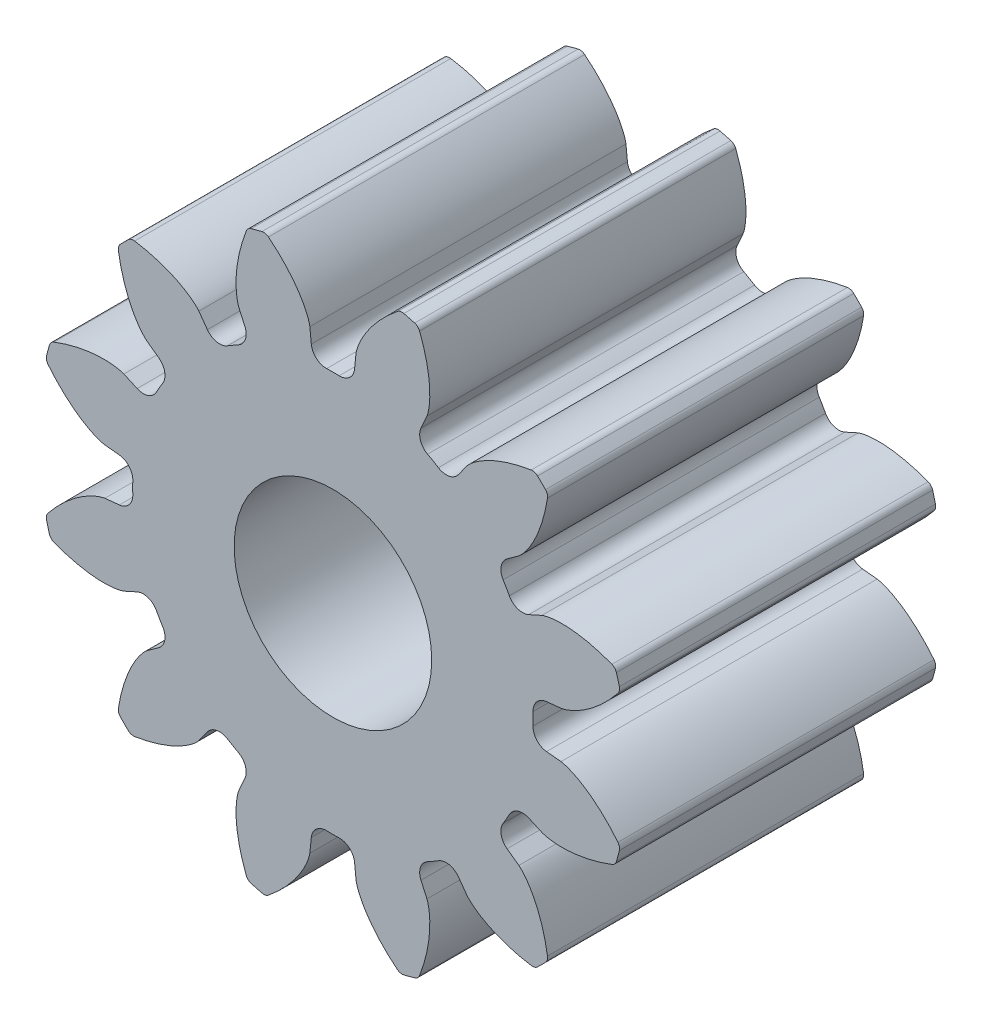
SolidWorks part; units mm, degrees
material "DELRIN"
ref_plane "Front" through (0, 0, 0) normal (0, 0, 1) x (1, 0, 0)
ref_plane "Top" through (0, 0, 0) normal (0, 1, 0) x (1, 0, 0)
ref_plane "Right" through (0, 0, 0) normal (1, 0, 0) x (0, 0, -1)
sketch "Sketch1" plane through (0, 0, 0) normal (0, 0, 1) x (1, 0, 0)
  circle A0 centre (0, 0) radius 11.8533
extrude "Boss-Extrude1" add sketch "Sketch1" along normal blind 12.7
sketch "Sketch3" plane through (0, 0, 0) normal (0, 0, 1) x (1, 0, 0)
  line L0 (0, 0) -> (43.7181, 0) construction
  line L2 (0, 0) -> (-0.8104, 8.0024) construction
  line L3 (0, 0) -> (0.8104, 8.0024) construction
  line L4 (0.8104, 8.0024) -> (0.9277, 9.1612) construction
  line L5 (0, 0) -> (0, 61.276) construction
  line L6 (-0.8104, 8.0024) -> (-0.9277, 9.1612) construction
  circle A0 centre (0, 0) radius 11.8533 construction
  circle A1 centre (0, 0) radius 10.16 construction
  circle A2 centre (0, 0) radius 9.2081 construction
  arc A3 (0.8104, 8.0024) -> (-0.8104, 8.0024) centre (0, 0) ccw construction
  arc A5 (2.7064, 11.5402) -> (-2.7064, 11.5402) centre (0, 0) ccw
  spline S0 degree 4 poles (-0.9277, 9.1612) (-0.9283, 9.1657) (-0.93, 9.1781) (-0.9342, 9.2015) (-0.9423, 9.2394) (-0.9545, 9.2874) (-0.9726, 9.3489) (-0.9967, 9.4206) (-1.026, 9.4987) (-1.0611, 9.5826) (-1.0988, 9.6655) (-1.1389, 9.7473) (-1.1812, 9.8279) (-1.235, 9.9246) (-1.3032, 10.0389) (-1.3882, 10.1702) (-1.4906, 10.3162) (-1.6015, 10.4617) (-1.7158, 10.602) (-1.8371, 10.7404) (-1.9586, 10.8719) (-2.0907, 11.0047) (-2.2156, 11.1255) (-2.3617, 11.2564) (-2.4815, 11.3607) (-2.6459, 11.4936) (-2.7449, 11.5706) (-2.863, 11.659) (-2.9166, 11.6974) (-2.9495, 11.721) knots 0 0 0 0 0 0.005377 0.015084 0.028532 0.04661 0.064855 0.092111 0.119476 0.146842 0.174209 0.201575 0.228941 0.256307 0.307035 0.361767 0.4165 0.471232 0.525964 0.580697 0.635429 0.690161 0.744894 0.799626 0.854358 0.909091 0.954545 1 1 1 1 1 construction
  spline S1 degree 4 poles (-0.9277, 9.1612) (-0.9283, 9.1657) (-0.93, 9.1781) (-0.9342, 9.2015) (-0.9423, 9.2394) (-0.9545, 9.2874) (-0.9726, 9.3489) (-0.9967, 9.4206) (-1.026, 9.4987) (-1.0611, 9.5826) (-1.0988, 9.6655) (-1.1389, 9.7473) (-1.1812, 9.8279) (-1.235, 9.9246) (-1.3032, 10.0389) (-1.3882, 10.1702) (-1.4906, 10.3162) (-1.6015, 10.4617) (-1.7158, 10.602) (-1.8371, 10.7404) (-1.9586, 10.8719) (-2.0907, 11.0047) (-2.2156, 11.1255) (-2.3617, 11.2564) (-2.4815, 11.3607) (-2.6102, 11.4648) (-2.6737, 11.5149) (-2.7064, 11.5402) knots 0 0 0 0 0 0.005377 0.015084 0.028532 0.04661 0.064855 0.092111 0.119476 0.146842 0.174209 0.201575 0.228941 0.256307 0.307035 0.361767 0.4165 0.471232 0.525964 0.580697 0.635429 0.690161 0.744894 0.799626 0.854358 0.909091 0.909091 0.909091 0.909091 0.909091
  spline S2 degree 4 poles (0.9277, 9.1612) (0.9283, 9.1657) (0.93, 9.1781) (0.9342, 9.2015) (0.9423, 9.2394) (0.9545, 9.2874) (0.9726, 9.3489) (0.9967, 9.4206) (1.026, 9.4987) (1.0611, 9.5826) (1.0988, 9.6655) (1.1389, 9.7473) (1.1812, 9.8279) (1.235, 9.9246) (1.3032, 10.0389) (1.3882, 10.1702) (1.4906, 10.3162) (1.6015, 10.4617) (1.7158, 10.602) (1.8371, 10.7404) (1.9586, 10.8719) (2.0907, 11.0047) (2.2156, 11.1255) (2.3617, 11.2564) (2.4815, 11.3607) (2.6459, 11.4936) (2.7449, 11.5706) (2.863, 11.659) (2.9166, 11.6974) (2.9495, 11.721) knots 0 0 0 0 0 0.005377 0.015084 0.028532 0.04661 0.064855 0.092111 0.119476 0.146842 0.174209 0.201575 0.228941 0.256307 0.307035 0.361767 0.4165 0.471232 0.525964 0.580697 0.635429 0.690161 0.744894 0.799626 0.854358 0.909091 0.954545 1 1 1 1 1 construction
  spline S3 degree 4 poles (0.9277, 9.1612) (0.9283, 9.1657) (0.93, 9.1781) (0.9342, 9.2015) (0.9423, 9.2394) (0.9545, 9.2874) (0.9726, 9.3489) (0.9967, 9.4206) (1.026, 9.4987) (1.0611, 9.5826) (1.0988, 9.6655) (1.1389, 9.7473) (1.1812, 9.8279) (1.235, 9.9246) (1.3032, 10.0389) (1.3882, 10.1702) (1.4906, 10.3162) (1.6015, 10.4617) (1.7158, 10.602) (1.8371, 10.7404) (1.9586, 10.8719) (2.0907, 11.0047) (2.2156, 11.1255) (2.3617, 11.2564) (2.4815, 11.3607) (2.6102, 11.4648) (2.6737, 11.5149) (2.7064, 11.5402) knots 0 0 0 0 0 0.005377 0.015084 0.028532 0.04661 0.064855 0.092111 0.119476 0.146842 0.174209 0.201575 0.228941 0.256307 0.307035 0.361767 0.4165 0.471232 0.525964 0.580697 0.635429 0.690161 0.744894 0.799626 0.854358 0.909091 0.909091 0.909091 0.909091 0.909091
  point P0 (0, 8.0433)
sketch "DCLTBC" plane through (0, 0, 0) normal (0, 0, 1) x (1, 0, 0)
  line L0 (0, 0) -> (41.04, 0) construction
  line L1 (-0.8104, 8.0024) -> (-0.9277, 9.1612) construction
  line L2 (0.8104, 8.0024) -> (0.9277, 9.1612) construction
  line L3 (-0.8104, 8.0024) -> (-0.9277, 9.1612)
  line L4 (0.8104, 8.0024) -> (0.9277, 9.1612)
  line L5 (0, 0) -> (0, 104.9356) construction
  circle A0 centre (0, 0) radius 11.8533
  circle A1 centre (0, 0) radius 10.16 construction
  circle A2 centre (0, 0) radius 9.2081 construction
  arc A3 (0.8104, 8.0024) -> (-0.8104, 8.0024) centre (0, 0) ccw construction
  arc A4 (0.8104, 8.0024) -> (-0.8104, 8.0024) centre (0, 0) ccw
  spline S0 degree 4 poles (-994.4739, -104.1267) (-14.2903, 6.4195) (-1.0522, 8.2498) (-0.8415, 8.7688) (-0.9423, 9.2394) (-0.9545, 9.2874) (-0.9726, 9.3489) (-0.9967, 9.4206) (-1.026, 9.4987) (-1.0611, 9.5826) (-1.0988, 9.6655) (-1.1389, 9.7473) (-1.1812, 9.8279) (-1.235, 9.9246) (-1.3032, 10.0389) (-1.3882, 10.1702) (-1.4906, 10.3162) (-1.6015, 10.4617) (-1.7158, 10.602) (-1.8371, 10.7404) (-1.9586, 10.8719) (-2.0907, 11.0047) (-2.2156, 11.1255) (-2.3617, 11.2564) (-2.9486, 11.7679) (-5.0034, 13.2442) (18.8088, -5.4292) (-793.4231, 623.6867) knots -0.531769 -0.531769 -0.531769 -0.531769 -0.531769 0.005377 0.015084 0.028532 0.04661 0.064855 0.092111 0.119476 0.146842 0.174209 0.201575 0.228941 0.256307 0.307035 0.361767 0.4165 0.471232 0.525964 0.580697 0.635429 0.690161 0.744894 0.799626 0.854358 1.763028 1.763028 1.763028 1.763028 1.763028 only from (-0.9277, 9.1612) to (-2.7064, 11.5402) construction
  spline S1 degree 4 poles (994.4739, -104.1267) (14.2903, 6.4195) (1.0522, 8.2498) (0.8415, 8.7688) (0.9423, 9.2394) (0.9545, 9.2874) (0.9726, 9.3489) (0.9967, 9.4206) (1.026, 9.4987) (1.0611, 9.5826) (1.0988, 9.6655) (1.1389, 9.7473) (1.1812, 9.8279) (1.235, 9.9246) (1.3032, 10.0389) (1.3882, 10.1702) (1.4906, 10.3162) (1.6015, 10.4617) (1.7158, 10.602) (1.8371, 10.7404) (1.9586, 10.8719) (2.0907, 11.0047) (2.2156, 11.1255) (2.3617, 11.2564) (2.9486, 11.7679) (5.0034, 13.2442) (-18.8088, -5.4292) (793.4231, 623.6867) knots -0.531769 -0.531769 -0.531769 -0.531769 -0.531769 0.005377 0.015084 0.028532 0.04661 0.064855 0.092111 0.119476 0.146842 0.174209 0.201575 0.228941 0.256307 0.307035 0.361767 0.4165 0.471232 0.525964 0.580697 0.635429 0.690161 0.744894 0.799626 0.854358 1.763028 1.763028 1.763028 1.763028 1.763028 only from (0.9277, 9.1612) to (2.7064, 11.5402) construction
  spline S2 degree 4 poles (-0.9277, 9.1612) (-0.9283, 9.1657) (-0.93, 9.1781) (-0.9342, 9.2015) (-0.9423, 9.2394) (-0.9545, 9.2874) (-0.9726, 9.3489) (-0.9967, 9.4206) (-1.026, 9.4987) (-1.0611, 9.5826) (-1.0988, 9.6655) (-1.1389, 9.7473) (-1.1812, 9.8279) (-1.235, 9.9246) (-1.3032, 10.0389) (-1.3882, 10.1702) (-1.4906, 10.3162) (-1.6015, 10.4617) (-1.7158, 10.602) (-1.8371, 10.7404) (-1.9586, 10.8719) (-2.0907, 11.0047) (-2.2156, 11.1255) (-2.3617, 11.2564) (-2.4815, 11.3607) (-2.6102, 11.4648) (-2.6737, 11.5149) (-2.7064, 11.5402) knots 0 0 0 0 0 0.005377 0.015084 0.028532 0.04661 0.064855 0.092111 0.119476 0.146842 0.174209 0.201575 0.228941 0.256307 0.307035 0.361767 0.4165 0.471232 0.525964 0.580697 0.635429 0.690161 0.744894 0.799626 0.854358 0.909091 0.909091 0.909091 0.909091 0.909091
  spline S3 degree 4 poles (0.9277, 9.1612) (0.9283, 9.1657) (0.93, 9.1781) (0.9342, 9.2015) (0.9423, 9.2394) (0.9545, 9.2874) (0.9726, 9.3489) (0.9967, 9.4206) (1.026, 9.4987) (1.0611, 9.5826) (1.0988, 9.6655) (1.1389, 9.7473) (1.1812, 9.8279) (1.235, 9.9246) (1.3032, 10.0389) (1.3882, 10.1702) (1.4906, 10.3162) (1.6015, 10.4617) (1.7158, 10.602) (1.8371, 10.7404) (1.9586, 10.8719) (2.0907, 11.0047) (2.2156, 11.1255) (2.3617, 11.2564) (2.4815, 11.3607) (2.6102, 11.4648) (2.6737, 11.5149) (2.7064, 11.5402) knots 0 0 0 0 0 0.005377 0.015084 0.028532 0.04661 0.064855 0.092111 0.119476 0.146842 0.174209 0.201575 0.228941 0.256307 0.307035 0.361767 0.4165 0.471232 0.525964 0.580697 0.635429 0.690161 0.744894 0.799626 0.854358 0.909091 0.909091 0.909091 0.909091 0.909091
extrude "Cut-Extrude-DCLTBC" cut sketch "DCLTBC" along normal through all
fillet "Fillet-Tip-DCLTBC" radius 0.3011 2 edges at (2.7064, 11.5402, 6.35) (-2.7064, 11.5402, 6.35)
fillet "Fillet-Root-DCLTBC" radius 0.6022 2 edges at (-0.8104, 8.0024, 6.35) (0.8104, 8.0024, 6.35)
pattern_circular "CirPattern-DCLTBC" count 12 over 360 about axis through (0, 0, 12.7) along (0, 0, 1) of "Cut-Extrude-DCLTBC", "Fillet-Tip-DCLTBC", "Fillet-Root-DCLTBC"
sketch "DCGTBC" [suppressed] plane through (0, 0, 0) normal (0, 0, 1) x (1, 0, 0)
  line L0 (0, 0) -> (41.04, 0) construction
  line L1 (-60.6226, 5.3038) -> (0, 0) construction
  line L2 (0, 0) -> (60.6226, 5.3038) construction
  line L3 (0, 0) -> (-16.5124, 0)
  line L5 (0, 0) -> (0, 104.9356) construction
  circle A0 centre (0, 0) radius 65.6167
  circle A1 centre (0, 0) radius 63.5 construction
  circle A2 centre (0, 0) radius 57.5505 construction
  arc A3 (-0.231, 60.8537) -> (0.231, 60.8537) centre (0, 0) ccw construction
  arc A11 (60.6226, 5.3038) -> (-60.6226, 5.3038) centre (0, 0) ccw
  spline S4 degree 4 poles (999.5281, 37.5164) (15.9379, 54.4029) (0.0707, 55.4419) (-0.2895, 56.6024) (-0.2066, 57.7767) (-0.1929, 57.9173) (-0.1708, 58.0988) (-0.1393, 58.3123) (-0.0988, 58.5468) (-0.0484, 58.8015) (0.0074, 59.0552) (0.0683, 59.3079) (0.1336, 59.5593) (0.2182, 59.8633) (0.3273, 60.227) (0.4659, 60.6511) (0.6363, 61.1305) (0.824, 61.6174) (1.0202, 62.0951) (1.2316, 62.5758) (1.4455, 63.0396) (1.6812, 63.5192) (1.9056, 63.9609) (2.1719, 64.4533) (3.0421, 66.0274) (5.6872, 70.2084) (-15.0429, 35.5301) (520.7458, 920.9699) knots -0.449335 -0.449335 -0.449335 -0.449335 -0.449335 0.005377 0.015084 0.028532 0.04661 0.064855 0.092111 0.119476 0.146842 0.174209 0.201575 0.228941 0.256307 0.307035 0.361767 0.4165 0.471232 0.525964 0.580697 0.635429 0.690161 0.744894 0.799626 0.854358 1.559054 1.559054 1.559054 1.559054 1.559054 only from (-0.2184, 57.5501) to (2.8092, 65.5565) construction
  spline S5 degree 4 poles (-999.5281, 37.5164) (-15.9379, 54.4029) (-0.0707, 55.4419) (0.2895, 56.6024) (0.2066, 57.7767) (0.1929, 57.9173) (0.1708, 58.0988) (0.1393, 58.3123) (0.0988, 58.5468) (0.0484, 58.8015) (-0.0074, 59.0552) (-0.0683, 59.3079) (-0.1336, 59.5593) (-0.2182, 59.8633) (-0.3273, 60.227) (-0.4659, 60.6511) (-0.6363, 61.1305) (-0.824, 61.6174) (-1.0202, 62.0951) (-1.2316, 62.5758) (-1.4455, 63.0396) (-1.6812, 63.5192) (-1.9056, 63.9609) (-2.1719, 64.4533) (-3.0421, 66.0274) (-5.6872, 70.2084) (15.0429, 35.5301) (-520.7458, 920.9699) knots -0.449335 -0.449335 -0.449335 -0.449335 -0.449335 0.005377 0.015084 0.028532 0.04661 0.064855 0.092111 0.119476 0.146842 0.174209 0.201575 0.228941 0.256307 0.307035 0.361767 0.4165 0.471232 0.525964 0.580697 0.635429 0.690161 0.744894 0.799626 0.854358 1.559054 1.559054 1.559054 1.559054 1.559054 only from (0.2184, 57.5501) to (-2.8092, 65.5565) construction
  spline S6 degree 4 poles (-0.2184, 57.5501) (-0.2183, 57.5629) (-0.2176, 57.5987) (-0.2144, 57.6663) (-0.2066, 57.7767) (-0.1929, 57.9173) (-0.1708, 58.0988) (-0.1393, 58.3123) (-0.0988, 58.5468) (-0.0484, 58.8015) (0.0074, 59.0552) (0.0683, 59.3079) (0.1336, 59.5593) (0.2182, 59.8633) (0.3273, 60.227) (0.4659, 60.6511) (0.6363, 61.1305) (0.824, 61.6174) (1.0202, 62.0951) (1.2316, 62.5758) (1.4455, 63.0396) (1.6812, 63.5192) (1.9056, 63.9609) (2.1719, 64.4533) (2.3911, 64.8499) (2.63, 65.2574) (2.7481, 65.4554) (2.8092, 65.5565) knots 0 0 0 0 0 0.005377 0.015084 0.028532 0.04661 0.064855 0.092111 0.119476 0.146842 0.174209 0.201575 0.228941 0.256307 0.307035 0.361767 0.4165 0.471232 0.525964 0.580697 0.635429 0.690161 0.744894 0.799626 0.854358 0.909091 0.909091 0.909091 0.909091 0.909091
  spline S7 degree 4 poles (0.2184, 57.5501) (0.2183, 57.5629) (0.2176, 57.5987) (0.2144, 57.6663) (0.2066, 57.7767) (0.1929, 57.9173) (0.1708, 58.0988) (0.1393, 58.3123) (0.0988, 58.5468) (0.0484, 58.8015) (-0.0074, 59.0552) (-0.0683, 59.3079) (-0.1336, 59.5593) (-0.2182, 59.8633) (-0.3273, 60.227) (-0.4659, 60.6511) (-0.6363, 61.1305) (-0.824, 61.6174) (-1.0202, 62.0951) (-1.2316, 62.5758) (-1.4455, 63.0396) (-1.6812, 63.5192) (-1.9056, 63.9609) (-2.1719, 64.4533) (-2.3911, 64.8499) (-2.63, 65.2574) (-2.7481, 65.4554) (-2.8092, 65.5565) knots 0 0 0 0 0 0.005377 0.015084 0.028532 0.04661 0.064855 0.092111 0.119476 0.146842 0.174209 0.201575 0.228941 0.256307 0.307035 0.361767 0.4165 0.471232 0.525964 0.580697 0.635429 0.690161 0.744894 0.799626 0.854358 0.909091 0.909091 0.909091 0.909091 0.909091
  dimension "D1" = 5
  dimension "D2" = 5
extrude "Cut-Extrude-DCGTBC" [suppressed] cut sketch "DCGTBC" along normal through all
fillet "Fillet-Tip-DCGTBC" [suppressed] radius 0.3011
pattern_circular "CirPattern-DCGTBC" [suppressed] count 12 over 360
sketch "Sketch8" plane through (0, 0, 0) normal (0, 0, 1) x (1, 0, 0)
  line L0 (18.125, -4.6) -> (21.725, -4.6)
  circle A2 centre (19.925, -7) radius 3
  circle A3 centre (0, 0) radius 3.9688
  dimension "D1" = 6
  dimension "13mm" = 7.9375
  dimension "D3" = 3.6
extrude "Cut-Extrude5" cut sketch "Sketch8" along normal blind 25.4
equation "\"DiametralPitch\"= 15'Diametral Pitch"
equation "\"NumTeeth\"= 12'Number of Teeth"
equation "\"PressureAngle\"= 25deg'Pressure Angle"
equation "\"Addendum\"= 1 / \"DiametralPitch\"'Addendum"
equation "\"Dedendum\"= 1.25 / \"DiametralPitch\"'Dedendum"
equation "\"WorkingDepth\"= 2 / \"DiametralPitch\"'Working Depth - here for REF (Not used in building model)"
equation "\"WholeDepth\"= 2.25 / \"DiametralPitch\"'Whole Depth - here for REF (Not used in building model)"
equation "\"Clearance\"= .25 / \"DiametralPitch\"'Clearance"
equation "\"CircularPitch\"= pi / \"DiametralPitch\"'Circular Pitch - here for REF (Not used in building model)"
equation "\"PitchCircle\"= \"NumTeeth\" / \"DiametralPitch\"'Pitch Circle - or - Pitch Diameter"
equation "\"OutsideDiameter\"= ( \"NumTeeth\" + 2 ) / \"DiametralPitch\"'Outside Diameter"
equation "\"Fillet_Root\"= \"Clearance\" * cos ( \"PressureAngle\" ) * tan ( ( 90 + \"PressureAngle\" ) / 2 ) 'Fillet Root"
equation "\"AddendumCircle\"= \"PitchCircle\" + ( 2 * \"Addendum\" )'Addendum Circle - or - Addendum Diameter"
equation "\"DedendumCircle\"= \"PitchCircle\" - ( 2 * \"Dedendum\" )'Dedendum Circle - or - Dedendum Diameter"
equation "\"BaseCircle\"= \"PitchCircle\" * cos ( \"PressureAngle\" )'Base Circle - Base Diameter"
equation "\"PitchAngle\"= 360deg / \"NumTeeth\"'Pitch Angle"
equation "\"Alpha\"= sqr ( \"PitchCircle\" ^ 2 - \"BaseCircle\" ^ 2 ) / \"BaseCircle\" * 180 / PI - \"PressureAngle\"'Alpha - Used for Calculating Beta"
equation "\"Beta\"= ( \"PitchAngle\" / 4 - ( \"Alpha\" - 90 ) )'Beta - Used in definition of the parameters for the parametric equation driven curve"
equation "\"Gamma\"= ( \"PitchAngle\" / 4 - ( \"Alpha\" + 90 ) )'Gamma - Used in definition of the parameters for the parametric equation driven curve"
equation "\"Phi\"= sqr ( ( \"AddendumCircle\" / 2 ) ^ 2 - ( \"BaseCircle\" / 2 ) ^ 2 ) / ( \"BaseCircle\" / 2 )'Phi - Used in definition of the parameters for the parametric equation driven curve"
equation "\"DCGTBC\"= iif ( \"DedendumCircle\" > \"BaseCircle\" , \"unsuppressed\" , \"suppressed\" )'if Dedendum Circle IS GREATER THAN BaseCircle THEN UnsuppressORSuppress FEATURE"
equation "\"DCLTBC\"= iif ( \"DedendumCircle\" - .002 > \"BaseCircle\" , \"suppressed\" , \"unsuppressed\" )'if Dedendum Circle - .002 IS GREATER THAN BaseCircle THEN SuppressORUnsuppress FEATURE"
equation "\"Cut-Extrude-DCGTBC\"= iif ( \"DedendumCircle\" > \"BaseCircle\" , \"unsuppressed\" , \"suppressed\" )'if Dedendum Circle IS GREATER THAN BaseCircle THEN UnsuppressORSuppress FEATURE"
equation "\"Cut-Extrude-DCLTBC\"= iif ( \"DedendumCircle\" - .002 > \"BaseCircle\" , \"suppressed\" , \"unsuppressed\" )'if Dedendum Circle - .002 IS GREATER THAN BaseCircle THEN SuppressORUnsuppress FEATURE"
equation "\"CirPattern-DCGTBC\"= iif ( \"DedendumCircle\" > \"BaseCircle\" , \"unsuppressed\" , \"suppressed\" )'if Dedendum Circle IS GREATER THAN BaseCircle THEN UnsuppressORSuppress FEATURE"
equation "\"CirPattern-DCLTBC\"= iif ( \"DedendumCircle\" - .002 > \"BaseCircle\" , \"suppressed\" , \"unsuppressed\" )'if Dedendum Circle - .002 IS GREATER THAN BaseCircle THEN SuppressORUnsuppress FEATURE"
equation "\"Fillet-Tip-DCGTBC\"= iif ( \"DedendumCircle\" > \"BaseCircle\" , \"unsuppressed\" , \"suppressed\" )'if Dedendum Circle IS GREATER THAN BaseCircle THEN UnsuppressORSuppress FEATURE"
equation "\"Fillet-Tip-DCLTBC\"= iif ( \"DedendumCircle\" - .002 > \"BaseCircle\" , \"suppressed\" , \"unsuppressed\" )'if Dedendum Circle - .002 IS GREATER THAN BaseCircle THEN SuppressORUnsuppress FEATURE"
equation "\"Fillet-Root-DCLTBC\"= iif ( \"DedendumCircle\" - .002 > \"BaseCircle\" , \"suppressed\" , \"unsuppressed\" )'if Dedendum Circle - .002 IS GREATER THAN BaseCircle THEN SuppressORUnsuppress FEATURE"
equation "\"D1@CirPattern-DCGTBC\"= \"NumTeeth\"'Number of Teeth"
equation "\"D1@CirPattern-DCLTBC\"= \"NumTeeth\"'Number of Teeth"
equation "\"D1@Fillet-Tip-DCGTBC\"= \"Fillet_Root\" / 2 'Tip Rad For Large No of Teeth"
equation "\"D1@Fillet-Tip-DCLTBC\"=\"Fillet_Root\" / 2'Tip Rad For Small No of Teeth"
equation "\"D1@Fillet-Root-DCLTBC\"= \"Fillet_Root\"'Fillet Root"
